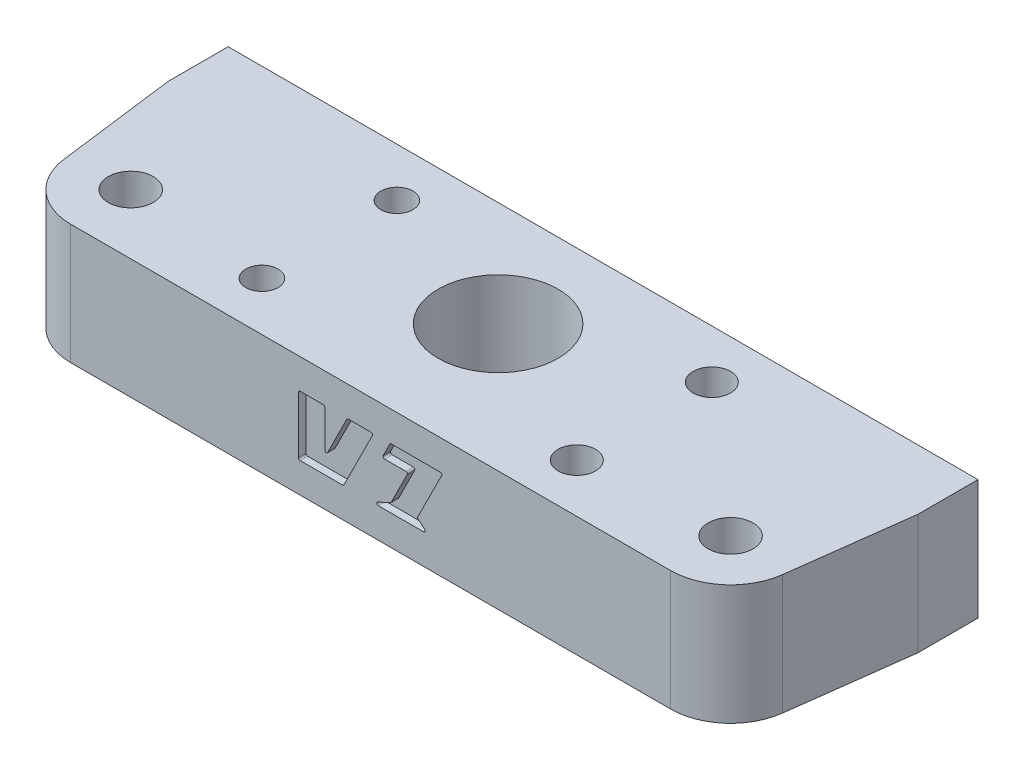
SolidWorks part; units mm, degrees
material "6061-T4 (SS)"
ref_plane "Front Plane" through (0, 0, 0) normal (0, 0, 1) x (1, 0, 0)
ref_plane "Top Plane" through (0, 0, 0) normal (0, 1, 0) x (1, 0, 0)
ref_plane "Right Plane" through (0, 0, 0) normal (1, 0, 0) x (0, 0, -1)
sketch "Sketch1" plane through (0, 0, 0) normal (0, 1, 0) x (1, 0, 0)
  line L0 (-40, 35) -> (40, 35) construction
  line L1 (0, 35) -> (0, 0) construction
  line L2 (-40, 57) -> (40, 57)
  line L4 (38.0933, -18.7323) -> (59.7421, 25.2918)
  line L5 (0, 35) -> (0, 57) construction
  line L6 (0, 0) -> (-47.2553, 0)
  line L7 (-41.2553, -10) -> (-47.2553, -10)
  line L8 (-47.2553, -10) -> (-47.2553, 0)
  line L11 (-47.2553, 3) -> (-32.311, 3)
  line L12 (-47.2553, 3) -> (-59.1799, 24.2237)
  arc A0 (-32.45, 0) -> (-32.311, 3) centre (0, 0) ccw
  arc A1 (-41.2553, -10) -> (38.0933, -18.7323) centre (0, 0) ccw
  circle A2 centre (40, 35) radius 14
  circle A3 centre (-40, 35) radius 14
  arc A6 (-40, 57) -> (-59.1799, 24.2237) centre (-40, 35) ccw
  circle A7 centre (0, 44) radius 5
  arc A8 (59.7421, 25.2918) -> (40, 57) centre (40, 35) ccw
  dimension "D1" = 64.9
  dimension "D2" = 10
  dimension "D4" = 28
  dimension "D6" = 22
  dimension "D7" = 8
  dimension "D8" = 10
  dimension "D9" = 13
  dimension "D3" = 80
  dimension "D5" = 35
  dimension "D10" = 10
  dimension "D11" = 6
  dimension "D12" = 3
extrude "Boss-Extrude1" add sketch "Sketch1" along normal blind 38 contours L4 A8 L2 A6 L12 L11 A0 L6 L8 L7 A1 A2 A3 A7
sketch "Sketch2" plane through (0, 38, 0) normal (0, 1, 0) x (1, 0, 0)
  line L0 (0, 0) -> (0, -38.8647) construction
  line L1 (-40, 57) -> (40, 57) construction
  line L2 (-40, 27) -> (40, 27)
  line L3 (-50, 58) -> (-50, 50)
  line L4 (50, 58) -> (50, 50)
  line L7 (-50, 50) -> (-47.9343, 33.9771)
  line L8 (-50, 58) -> (50, 58)
  line L9 (50, 50) -> (47.9343, 33.9771)
  circle A6 centre (0, 44) radius 8
  circle A7 centre (-40, 35) radius 3
  circle A8 centre (40, 35) radius 3
  circle A10 centre (-40, 35) radius 14 construction
  circle A11 centre (40, 35) radius 14 construction
  arc A18 (-47.9343, 33.9771) -> (-40, 27) centre (-40, 35) ccw
  arc A19 (40, 27) -> (47.9343, 33.9771) centre (40, 35) ccw
  point P22 (0, 58)
  dimension "D2" = 8
  dimension "D3" = 8
  dimension "D4" = 16
  dimension "D6" = 6
  dimension "D1" = 100
  dimension "D5" = 1
extrude "Boss-Extrude2" add sketch "Sketch2" along normal blind 16 separate body contours A19 L9 L8 L7 A18 L2 | A6
delete or keep bodies "Body-Delete/Keep 1" type delete bodies bodies 101
sketch "Sketch3" plane through (0, 0, -58) normal (0, 0, -1) x (-1, 0, 0)
  line L0 (-40, 46) -> (40, 46) construction
  line L2 (-50, 54) -> (50, 54) construction
  line L3 (-50, 38) -> (50, 38) construction
  line L4 (0, 54) -> (0, 38) construction
  circle A0 centre (-40, 46) radius 2.5
  circle A1 centre (40, 46) radius 2.5
  point P10 (0, 46)
  dimension "D2" = 5
  dimension "D1" = 80
extrude "Cut-Extrude1" cut sketch "Sketch3" against normal blind 21
sketch "Sketch4" plane through (0, 38, 0) normal (0, -1, 0) x (1, 0, 0)
  line L0 (0, -27) -> (0, -58) construction
  line L1 (-21, -33.5) -> (-21, -51.5) construction
  line L2 (-40, -27) -> (40, -27) construction
  line L3 (21, -33.5) -> (21, -51.5) construction
  line L4 (50, -58) -> (-50, -58) construction
  line L5 (-21, -42.5) -> (21, -42.5) construction
  circle A1 centre (-21, -33.5) radius 2.15
  circle A2 centre (-21, -51.5) radius 2.15
  circle A3 centre (21, -51.5) radius 2.5
  circle A4 centre (21, -33.5) radius 2.5
  point P18 (0, -42.5)
  dimension "D3" = 4.3
  dimension "D1" = 18
  dimension "D2" = 42
extrude "Cut-Extrude2" cut sketch "Sketch4" against normal blind 21
sketch "Sketch6" plane through (0, 0, -27) normal (0, 0, 1) x (1, 0, 0)
  line L0 (-9.618, 50) -> (-9.618, 42)
  line L1 (-9.618, 42) -> (-3.618, 42)
  line L2 (-3.618, 42) -> (0.382, 50)
  line L3 (0.382, 50) -> (-3.118, 50)
  line L4 (-3.118, 50) -> (-6.118, 44)
  line L5 (-6.118, 44) -> (-6.118, 50)
  line L6 (-6.118, 50) -> (-9.618, 50)
  line L7 (-9.618, 46) -> (9.618, 46) construction
  line L8 (-40, 54) -> (40, 54) construction
  line L9 (-40, 38) -> (40, 38) construction
  line L10 (2.618, 50) -> (1.518, 47.8)
  line L11 (1.518, 47.8) -> (5.018, 47.8)
  line L12 (5.018, 47.8) -> (2.718, 43.2)
  line L13 (2.118, 42) -> (5.618, 42)
  line L14 (6.218, 43.2) -> (9.618, 50)
  line L15 (9.618, 50) -> (2.618, 50)
  line L16 (0, 54) -> (0, 46) construction
  line L17 (2.718, 43.2) -> (0.118, 42)
  line L18 (0.118, 42) -> (7.618, 42)
  line L19 (7.618, 42) -> (6.218, 43.2)
  dimension "D1" = 8
  dimension "D2" = 6
  dimension "D3" = 3.5
  dimension "D4" = 3
  dimension "D5" = 2
  dimension "D6" = 3.5
  dimension "D7" = 3.5
  dimension "D8" = 2.2
  dimension "D9" = 2
  dimension "D10" = 2
  dimension "D11" = 1.2
extrude "Cut-Extrude3" cut sketch "Sketch6" against normal blind 1 contours L5 L6 L0 L1 L2 L3 L4 | L18 L19 L14 L15 L10 L11 L12 L17 L13
fillet "Fillet2" radius 0.2 15 edges at (9.618, 50, -27.5) (2.618, 50, -27.5) (1.518, 47.8, -27.5) (5.018, 47.8, -27.5) (-9.618, 42, -27.5) (0.382, 50, -27.5) (-3.118, 50, -27.5) (-6.118, 44, -27.5) (-6.118, 50, -27.5) (-9.618, 50, -27.5) (-3.618, 42, -27.5) (6.218, 43.2, -27.5) (2.718, 43.2, -27.5) (0.118, 42, -27.5) (7.618, 42, -27.5)
